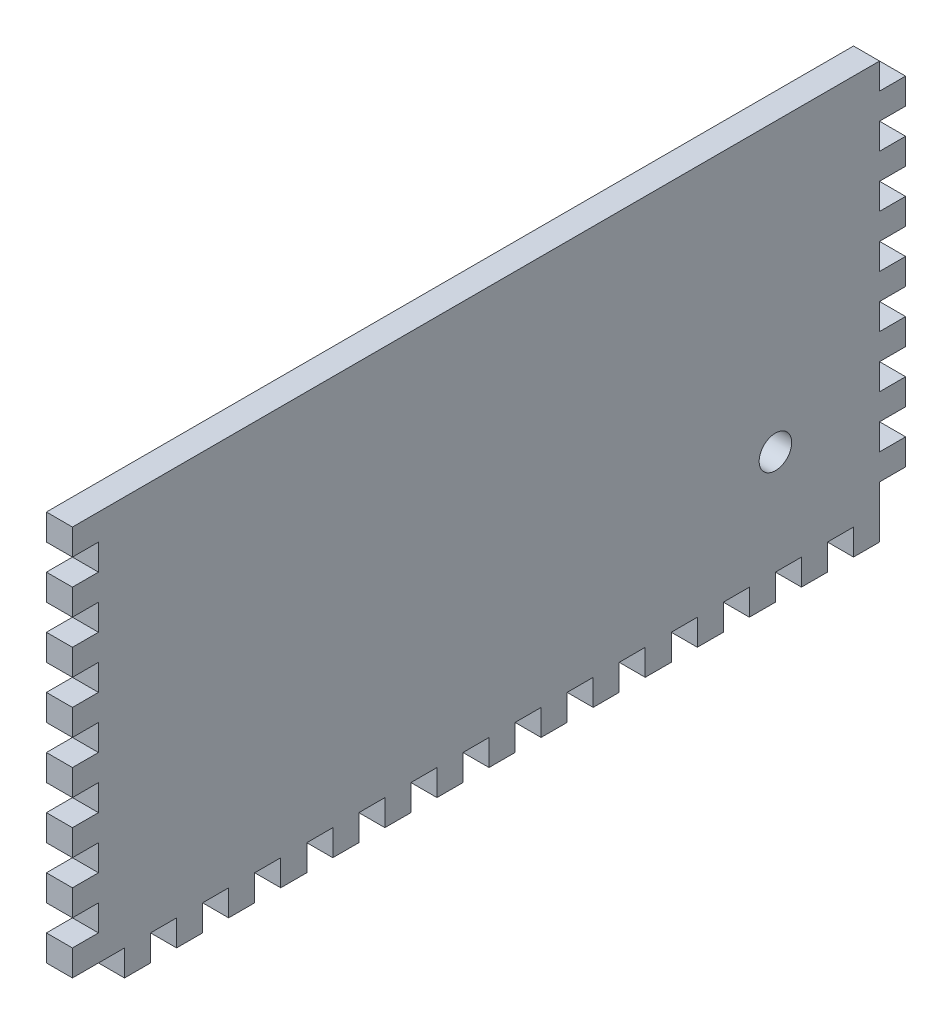
SolidWorks part; units mm, degrees
ref_plane "Front Plane" through (0, 0, 0) normal (0, 0, 1) x (1, 0, 0)
ref_plane "Top Plane" through (0, 0, 0) normal (0, 1, 0) x (1, 0, 0)
ref_plane "Right Plane" through (0, 0, 0) normal (1, 0, 0) x (0, 0, -1)
sketch "Sketch1" plane through (0, 0, 0) normal (1, 0, 0) x (0, 0, -1)
  line L1 (0, 0) -> (203.2, 0)
  line L2 (0, 0) -> (0, 101.6)
  line L3 (0, 101.6) -> (203.2, 101.6)
  line L4 (203.2, 0) -> (203.2, 101.6)
  dimension "D1" = 203.2
  dimension "D2" = 101.6
extrude "Boss-Extrude1" add sketch "Sketch1" along normal blind 6.35 contours L3 L4 L1 L2
sketch "Sketch3" plane through (0, 0, 0) normal (0, -1, 0) x (1, 0, 0)
  line L0 (6.35, 0) -> (6.35, -203.2) construction
  line L2 (0, 0) -> (6.35, 0)
  line L3 (0, 0) -> (0, -12.7)
  line L4 (0, -12.7) -> (6.35, -12.7)
  line L5 (6.35, 0) -> (6.35, -12.7)
extrude "Cut-Extrude2" cut sketch "Sketch3" against normal blind 6.35
sketch "Sketch4" plane through (0, 0, 0) normal (0, -1, 0) x (1, 0, 0)
  line L0 (6.35, -12.7) -> (6.35, -203.2) construction
  line L1 (6.35, -19.05) -> (0, -19.05)
  line L2 (6.35, -19.05) -> (6.35, -25.4)
  line L3 (6.35, -25.4) -> (0, -25.4)
  line L4 (0, -19.05) -> (0, -25.4)
  line L5 (0, -12.7) -> (0, -203.2) construction
extrude "Cut-Extrude3" cut sketch "Sketch4" against normal blind 6.35
pattern_linear "LPattern1" count 15 spacing 12.7 along (0, 0, -1) of "Cut-Extrude3"
sketch "Sketch5" plane through (0, 0, 0) normal (0, 0, 1) x (1, 0, 0)
  line L0 (6.35, 6.35) -> (6.35, 101.6) construction
  line L1 (6.35, 12.7) -> (0, 12.7)
  line L2 (6.35, 12.7) -> (6.35, 19.05)
  line L3 (6.35, 19.05) -> (0, 19.05)
  line L4 (0, 12.7) -> (0, 19.05)
  line L5 (0, 6.35) -> (0, 101.6) construction
extrude "Cut-Extrude4" cut sketch "Sketch5" against normal blind 6.35
pattern_linear "LPattern2" count 7 spacing 12.7 along (0, 1, 0) of "Cut-Extrude4"
sketch "Sketch6" plane through (0, 0, -203.2) normal (0, 0, -1) x (-1, 0, 0)
  line L0 (-6.35, 6.35) -> (-6.35, 101.6) construction
  line L1 (0, 6.35) -> (-6.35, 6.35)
  line L2 (0, 6.35) -> (0, 12.7)
  line L3 (0, 12.7) -> (-6.35, 12.7)
  line L4 (-6.35, 6.35) -> (-6.35, 12.7)
extrude "Cut-Extrude5" cut sketch "Sketch6" against normal blind 6.35
sketch "Sketch8" plane through (0, 0, -203.2) normal (0, 0, -1) x (-1, 0, 0)
  line L0 (0, 12.7) -> (0, 101.6) construction
  line L1 (0, 19.05) -> (-6.35, 19.05)
  line L2 (0, 19.05) -> (0, 25.4)
  line L3 (0, 25.4) -> (-6.35, 25.4)
  line L4 (-6.35, 19.05) -> (-6.35, 25.4)
  line L5 (-6.35, 12.7) -> (-6.35, 101.6) construction
extrude "Cut-Extrude6" cut sketch "Sketch8" against normal blind 6.35
pattern_linear "LPattern3" count 7 spacing 12.7 along (0, 1, 0) of "Cut-Extrude6"
sketch "Sketch9" plane through (0, 0, 0) normal (-1, 0, 0) x (0, 0, 1)
  line L1 (-165.1, 0) -> (-171.45, 0) construction
  line L2 (-203.2, 25.4) -> (-203.2, 31.75) construction
  circle A0 centre (-171.45, 31.75) radius 3.9687
  point P4 (-168.275, 0)
  dimension "D1" = 7.9375
  dimension "D2" = 31.75
  dimension "D3" = 31.75
extrude "Cut-Extrude7" cut sketch "Sketch9" against normal blind 6.35
